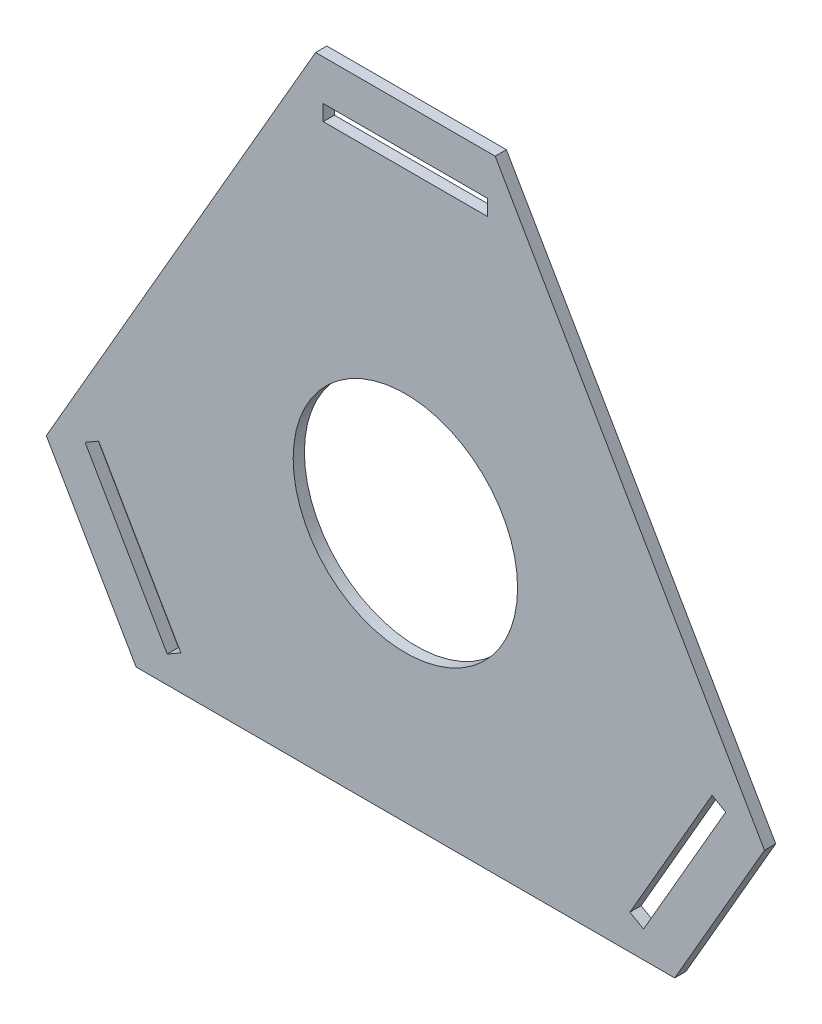
SolidWorks part; units mm, degrees
ref_plane "Front Plane" through (0, 0, 0) normal (0, 0, 1) x (1, 0, 0)
ref_plane "Top Plane" through (0, 0, 0) normal (0, 1, 0) x (1, 0, 0)
ref_plane "Right Plane" through (0, 0, 0) normal (1, 0, 0) x (0, 0, -1)
sketch "Sketch1" plane through (0, 0, 0) normal (0, 0, 1) x (1, 0, 0)
  line L0 (0, 0) -> (240, 0)
  line L1 (240, 0) -> (280, 69.282)
  line L2 (280, 69.282) -> (160, 277.1281)
  line L3 (160, 277.1281) -> (80, 277.1281)
  line L4 (80, 277.1281) -> (-40, 69.282)
  line L5 (-40, 69.282) -> (0, 0)
  line L10 (149.6077, 259.1281) -> (90.3923, 259.1281)
  line L16 (145.5662, 252.1281) -> (94.4338, 252.1281)
  line L18 (90.3923, 259.1281) -> (-19.2154, 69.282) construction
  line L19 (94.4338, 252.1281) -> (-11.1325, 69.282) construction
  line L20 (14.4338, 25) -> (225.5662, 25) construction
  line L21 (10.3923, 18) -> (229.6077, 18) construction
  line L22 (251.1325, 69.282) -> (145.5662, 252.1281) construction
  line L23 (259.2154, 69.282) -> (149.6077, 259.1281) construction
  line L24 (90.3923, 259.1281) -> (90.3923, 252.1281) construction
  line L25 (90.3923, 252.1281) -> (94.4338, 252.1281)
  line L26 (149.6077, 259.1281) -> (149.6077, 252.1281) construction
  line L27 (149.6077, 252.1281) -> (145.5662, 252.1281)
  line L29 (-11.1325, 69.282) -> (14.4338, 25) construction
  line L30 (-19.2154, 69.282) -> (10.3923, 18) construction
  line L31 (225.5662, 25) -> (251.1325, 69.282) construction
  line L32 (229.6077, 18) -> (259.2154, 69.282) construction
  line L44 (149.6077, 259.1281) -> (156.6077, 259.1281)
  line L45 (156.6077, 259.1281) -> (156.6077, 252.1281)
  line L46 (156.6077, 252.1281) -> (149.6077, 252.1281)
  line L47 (90.3923, 259.1281) -> (83.3923, 259.1281)
  line L48 (83.3923, 259.1281) -> (83.3923, 252.1281)
  line L49 (83.3923, 252.1281) -> (90.3923, 252.1281)
  line L50 (225.5662, 25) -> (251.1325, 69.282)
  line L51 (223.5455, 21.5) -> (225.5662, 25)
  line L52 (220.0455, 15.4378) -> (223.5455, 21.5)
  line L53 (226.1077, 11.9378) -> (220.0455, 15.4378)
  line L54 (229.6077, 18) -> (226.1077, 11.9378)
  line L55 (229.6077, 18) -> (259.2154, 69.282)
  line L56 (259.2154, 69.282) -> (262.7154, 75.3442)
  line L57 (262.7154, 75.3442) -> (256.6532, 78.8442)
  line L58 (256.6532, 78.8442) -> (253.1532, 72.782)
  line L59 (253.1532, 72.782) -> (251.1325, 69.282)
  line L60 (-11.1325, 69.282) -> (14.4338, 25)
  line L61 (-13.1532, 72.782) -> (-11.1325, 69.282)
  line L62 (-16.6532, 78.8442) -> (-13.1532, 72.782)
  line L63 (-22.7154, 75.3442) -> (-16.6532, 78.8442)
  line L64 (-19.2154, 69.282) -> (-22.7154, 75.3442)
  line L65 (-19.2154, 69.282) -> (10.3923, 18)
  line L66 (10.3923, 18) -> (13.8923, 11.9378)
  line L67 (13.8923, 11.9378) -> (19.9545, 15.4378)
  line L68 (19.9545, 15.4378) -> (16.4545, 21.5)
  line L69 (16.4545, 21.5) -> (14.4338, 25)
  circle A1 centre (120, 115.4701) radius 115.4701 construction
  circle A2 centre (120, 115.4701) radius 50
  point P38 (120, 115.4701)
  point P51 (120, 115.4701)
  dimension "D8" = 3
  dimension "D11" = 100
  dimension "D1" = 240
  dimension "D2" = 80
  dimension "D3" = 120
  dimension "D4" = 120
  dimension "D5" = 120
  dimension "D6" = 18
  dimension "D9" = 7
  dimension "D10" = 7
  dimension "D7" = 25
extrude "Boss-Extrude1" add sketch "Sketch1" along normal blind 5
sketch "Sketch2" plane through (0, 0, 5) normal (0, 0, 1) x (1, 0, 0)
  line L0 (-20, 34.641) -> (220, 173.2051)
  line L1 (-40, 69.282) -> (0, 0) construction
  line L2 (280, 69.282) -> (160, 277.1281) construction
  line L3 (260, 34.641) -> (20, 173.2051)
  line L4 (240, 0) -> (280, 69.282) construction
  line L5 (80, 277.1281) -> (-40, 69.282) construction
  line L6 (120, 0) -> (120, 277.1281)
  line L7 (0, 0) -> (240, 0) construction
  line L8 (160, 277.1281) -> (80, 277.1281) construction
